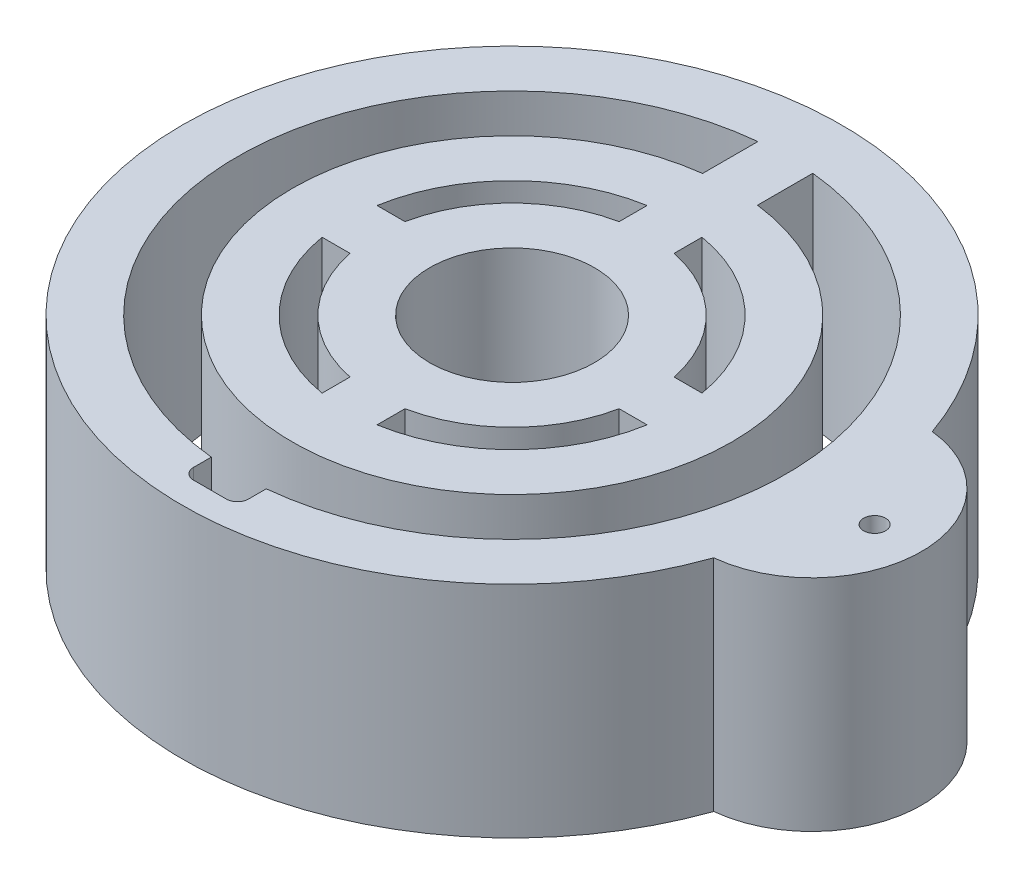
SolidWorks part; units mm, degrees
ref_plane "Front Plane" through (0, 0, 0) normal (0, 0, 1) x (1, 0, 0)
ref_plane "Top Plane" through (0, 0, 0) normal (0, 1, 0) x (1, 0, 0)
ref_plane "Right Plane" through (0, 0, 0) normal (1, 0, 0) x (0, 0, -1)
sketch "Sketch1" plane through (0, 0, 0) normal (0, 1, 0) x (1, 0, 0)
  line L2 (-2.5, 27.226) -> (-2.5, 16.7283)
  line L4 (2.5, 27.226) -> (2.5, 16.7283)
  line L5 (-2.5, -22.9334) -> (2.5, -22.9334)
  line L6 (-2.5, -22.9334) -> (-2.5, -26.5)
  line L7 (-1.5, -27.5) -> (1.5, -27.5)
  line L8 (2.5, -22.9334) -> (2.5, -26.5)
  arc A0 (-2.5, 19.8431) -> (2.5, 19.8431) centre (0, 0) ccw
  arc A1 (-2.5, 24.8747) -> (2.5, 24.8747) centre (0, 0) ccw
  circle A2 centre (0, 0) radius 30
  circle A3 centre (0, 0) radius 15
  arc A4 (-2.5, -26.5) -> (-1.5, -27.5) centre (-1.5, -26.5) ccw
  arc A5 (1.5, -27.5) -> (2.5, -26.5) centre (1.5, -26.5) ccw
  point P18 (-2.5, -27.5)
  point P21 (2.5, -27.5)
  dimension "D1" = 40
  dimension "D2" = 50
  dimension "D3" = 60
  dimension "D4" = 30
  dimension "D10" = 1
  dimension "D5" = 5
  dimension "D6" = 2.5
  dimension "D7" = 27.5
  dimension "D8" = 5
  dimension "D9" = 2.5
extrude "Boss-Extrude1" add sketch "Sketch1" along normal blind 20
sketch "Sketch2" plane through (0, 20, 0) normal (0, 1, 0) x (1, 0, 0)
  line L0 (27.2718, 10) -> (27.2718, -10)
  arc A0 (27.2718, 10) -> (27.2718, -10) centre (27.2718, 0) cw
  dimension "D2" = 10
  dimension "D1" = 20
extrude "Boss-Extrude2" add sketch "Sketch2" against normal blind 20
sketch "Sketch3" plane through (0, 20, 0) normal (0, 1, 0) x (1, 0, 0)
  circle A0 centre (33, 0) radius 1
  dimension "D1" = 2
  dimension "D2" = 33
extrude "Cut-Extrude1" cut sketch "Sketch3" against normal blind 20
sketch "Sketch4" plane through (0, 0, 0) normal (0, 1, 0) x (1, 0, 0)
  line L5 (2.5, 24.8747) -> (2.5, 19.8431) construction
  line L6 (-2.5, 19.8431) -> (2.5, 19.8431)
  line L7 (-2.5, 19.8431) -> (-2.5, 12.2474)
  line L9 (2.5, 19.8431) -> (2.5, 12.2474)
  line L11 (-12.2474, 2.5) -> (-16.9586, 2.5)
  line L13 (-12.2474, -2.5) -> (-16.9586, -2.5)
  line L14 (-16.9586, 2.5) -> (-16.9586, -2.5)
  line L16 (-2.5, -12.2474) -> (-2.5, -17.5757)
  line L17 (-2.5, -17.5757) -> (2.5, -17.5757)
  line L18 (2.5, -12.2474) -> (2.5, -17.5757)
  line L19 (12.2474, 2.5) -> (16.1249, 2.5)
  line L21 (12.2474, -2.5) -> (16.1249, -2.5)
  line L22 (16.1249, 2.5) -> (16.1249, -2.5)
  circle A1 centre (0, 0) radius 7.5
  arc A2 (2.5, -12.2474) -> (12.2474, -2.5) centre (0, 0) ccw
  arc A3 (-12.2474, -2.5) -> (-2.5, -12.2474) centre (0, 0) ccw
  arc A4 (-2.5, 12.2474) -> (-12.2474, 2.5) centre (0, 0) ccw
  arc A5 (12.2474, 2.5) -> (2.5, 12.2474) centre (0, 0) ccw
  dimension "D1" = 15
  dimension "D2" = 25
  dimension "D3" = 5
  dimension "D4" = 2.5
extrude "Boss-Extrude3" add sketch "Sketch4" along normal blind 20
